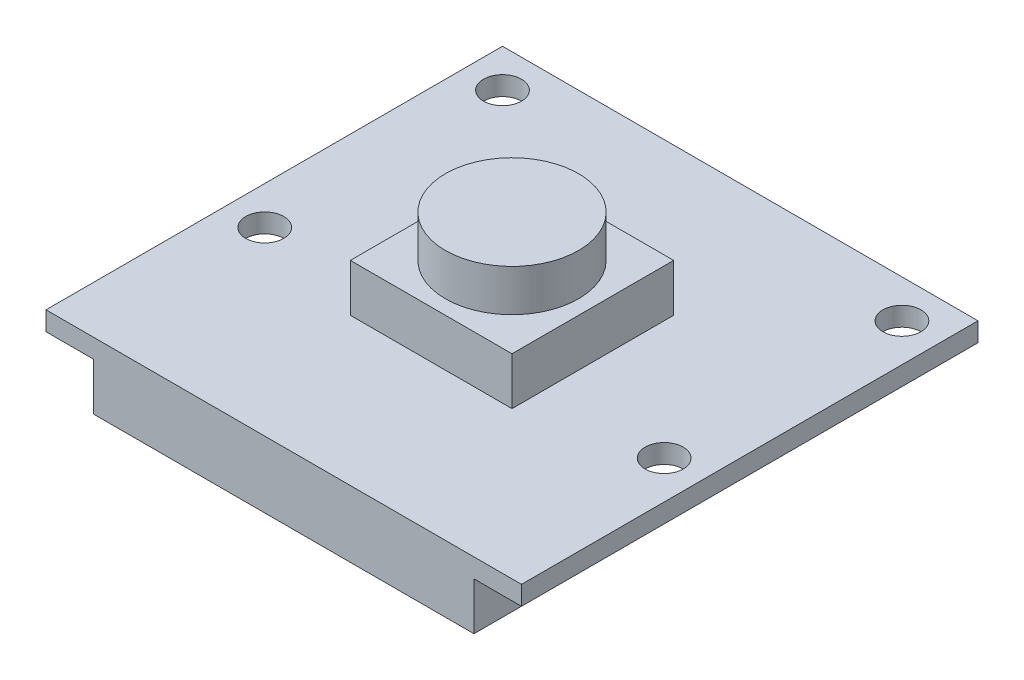
SolidWorks part; units mm, degrees
ref_plane "Front" through (0, 0, 0) normal (0, 0, 1) x (1, 0, 0)
ref_plane "Top" through (0, 0, 0) normal (0, 1, 0) x (1, 0, 0)
ref_plane "Right" through (0, 0, 0) normal (1, 0, 0) x (0, 0, -1)
sketch "Sketch1" plane through (0, 0, 0) normal (0, 1, 0) x (1, 0, 0)
  line L0 (12.5, 24) -> (12.5, 0) construction
  line L1 (0, 0) -> (25, 0)
  line L2 (0, 0) -> (0, 24)
  line L3 (0, 24) -> (25, 24)
  line L4 (25, 0) -> (25, 24)
  circle A0 centre (2, 22) radius 1
  circle A1 centre (2, 9.5) radius 1
  circle A2 centre (23, 9.5) radius 1
  circle A3 centre (23, 22) radius 1
  dimension "D5" = 2
  dimension "D4" = 1
  dimension "D6" = 10.5
  dimension "D1" = 25
  dimension "D2" = 24
  dimension "D3" = 1
extrude "Boss-Extrude1" add sketch "Sketch1" along normal blind 1
sketch "Sketch2" plane through (0, 1, 0) normal (0, 1, 0) x (1, 0, 0)
  line L0 (12.5, 24) -> (12.5, 0) construction
  line L1 (8.25, 16.25) -> (16.75, 16.25)
  line L2 (8.25, 16.25) -> (8.25, 7.75)
  line L3 (8.25, 7.75) -> (16.75, 7.75)
  line L4 (16.75, 16.25) -> (16.75, 7.75)
  line L5 (25, 24) -> (0, 24) construction
  line L6 (0, 0) -> (25, 0) construction
  line L7 (0, 24) -> (0, 0) construction
  point P10 (8.25, 12)
  point P13 (0, 12)
  point P14 (12.5, 16.25)
  dimension "D1" = 8.5
  dimension "D2" = 8.5
extrude "Boss-Extrude2" add sketch "Sketch2" along normal blind 2.5
sketch "Sketch3" plane through (0, 3.5, 0) normal (0, 1, 0) x (1, 0, 0)
  line L0 (16.75, 16.25) -> (8.25, 16.25) construction
  line L1 (16.75, 7.75) -> (16.75, 16.25) construction
  circle A0 centre (12.5, 12) radius 3.5
  point P5 (12.5, 16.25)
  point P9 (16.75, 12)
  dimension "D1" = 7
extrude "Boss-Extrude3" add sketch "Sketch3" along normal blind 2.2
sketch "Sketch4" plane through (0, 0, 0) normal (0, -1, 0) x (1, 0, 0)
  line L0 (0, 0) -> (25, 0) construction
  line L1 (2.5, 0) -> (22.5, 0)
  line L2 (2.5, 0) -> (2.5, -6)
  line L3 (2.5, -6) -> (22.5, -6)
  line L4 (22.5, 0) -> (22.5, -6)
  point P6 (12.5, 0)
  point P7 (12.5, 0)
  dimension "D1" = 6
  dimension "D2" = 20
extrude "Boss-Extrude4" add sketch "Sketch4" along normal blind 2.5
